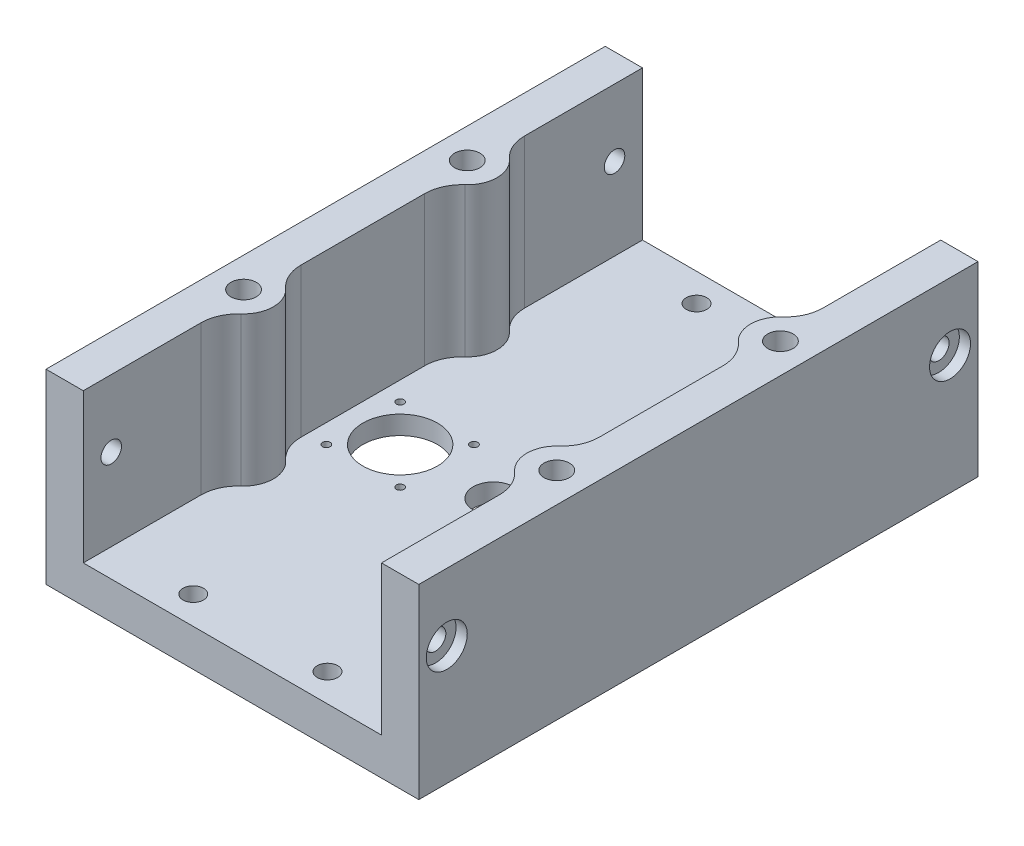
SolidWorks part; units mm, degrees
material "ERTALON 6SA"
ref_plane "Front Plane" through (0, 0, 0) normal (0, 0, 1) x (1, 0, 0)
ref_plane "Top Plane" through (0, 0, 0) normal (0, 1, 0) x (1, 0, 0)
ref_plane "Right Plane" through (0, 0, 0) normal (1, 0, 0) x (0, 0, -1)
sketch "Sketch1" plane through (0, 0, 0) normal (0, 1, 0) x (1, 0, 0)
  line L1 (-50, 0) -> (50, 0)
  line L2 (-50, 0) -> (-50, 150)
  line L3 (-50, 150) -> (50, 150)
  line L4 (50, 0) -> (50, 150)
  dimension "D1" = 100
  dimension "D2" = 50
  dimension "D3" = 150
extrude "Extrude1" add sketch "Sketch1" against normal blind 10
sketch "Sketch2" plane through (0, 0, 0) normal (0, 1, 0) x (1, 0, 0)
  line L0 (50, 150) -> (-50, 150) construction
  line L1 (-50, 150) -> (-40, 150)
  line L2 (-50, 150) -> (-50, 0)
  line L3 (-50, 0) -> (-40, 0)
  line L4 (-40, 150) -> (-40, 0)
  line L5 (-50, 0) -> (50, 0) construction
  line L6 (-50, 150) -> (-50, 0) construction
  line L7 (50, 0) -> (50, 150) construction
  line L8 (40, 150) -> (50, 150)
  line L9 (40, 150) -> (40, 0)
  line L10 (40, 0) -> (50, 0)
  line L11 (50, 150) -> (50, 0)
  dimension "D1" = 10
  dimension "D2" = 10
extrude "Extrude2" add sketch "Sketch2" along normal blind 40
sketch "Sketch6" plane through (0, 40, 0) normal (0, 1, 0) x (1, 0, 0)
  line L0 (50, 0) -> (50, 150) construction
  line L1 (42, 53) -> (50, 53)
  line L2 (50, 53) -> (50, 37)
  line L3 (50, 37) -> (42, 37)
  line L4 (50, 150) -> (40, 150) construction
  line L5 (42, 113) -> (50, 113)
  line L6 (50, 113) -> (50, 97)
  line L7 (50, 97) -> (42, 97)
  line L8 (40, 0) -> (50, 0) construction
  arc A0 (42, 53) -> (42, 37) centre (42, 45) ccw
  arc A1 (42, 113) -> (42, 97) centre (42, 105) ccw
  point P9 (45, 150)
  dimension "D1" = 8
  dimension "D2" = 45
  dimension "D3" = 45
extrude "Extrude5" add sketch "Sketch6" against normal up to next (50 mm away)
mirror "Mirror2" about plane through (0, 0, 0) normal (1, 0, 0) of "Extrude5"
fillet "Fillet1" radius 10 8 edges at (40, 20, -112.746) (40, 20, -97.254) (40, 20, -52.746) (40, 20, -37.254) (-40, 20, -97.254) (-40, 20, -112.746) (-40, 20, -37.254) (-40, 20, -52.746)
hole_wizard "M8 Tapped Hole1" positions "Sketch13" profile "Sketch12" tap size "M8" standard "ISO"
sketch "Sketch13" plane through (0, 40, 0) normal (0, 1, 0) x (-1, 0, 0)
  arc A0 (-36.6667, -50.9628) -> (-36.6667, -39.0372) centre (-42, -45) ccw construction
  point P0 (-42, -45)
sketch "Sketch12" plane through (42, 40, -45) normal (1, 0, 0) x (0, 0, 1)
  line L0 (0, 0) -> (0, 24.0429)
  line L1 (0, 24.0429) -> (3.4, 22)
  line L2 (3.4, 22) -> (3.4, 0)
  line L5 (3.4, 0) -> (0, 0)
  line L10 (0, 24.0429) -> (-3.4, 22) construction
  line L11 (0, -6.35) -> (0, 107.95) construction
  dimension "Tap Drill Dia." = 6.8
  dimension "Tap Drill Depth" = 22
  dimension "Drill Angle" = 118
cosmetic thread "Hole Thread2" parameters "D1"=16, "D2"=8
pattern_linear "LPattern1" count 2 spacing 60 along (0, 0, -1) count 2 spacing 84 along (-1, 0, 0) of "M8 Tapped Hole1"
ref_plane "Plane2" through (0, 0, -75) normal (0, 0, 1) x (1, 0, 0)
sketch "Sketch16" plane through (0, -10, 0) normal (0, -1, 0) x (1, 0, 0)
  line L1 (-40, -15) -> (40, -15)
  line L2 (-40, -15) -> (-40, -90)
  line L3 (-40, -90) -> (40, -90)
  line L4 (40, -15) -> (40, -90)
  line L6 (-50, 0) -> (50, 0) construction
  point P4 (0, -15)
  dimension "D1" = 75
  dimension "D2" = 80
  dimension "D3" = 15
extrude "Extrude8" cut sketch "Sketch16" against normal blind 5
fillet "Fillet2" radius 6 4 edges at (-40, -7.5, -15) (40, -7.5, -15) (-40, -7.5, -90) (40, -7.5, -90)
sketch "Sketch14" plane through (0, -10, 0) normal (0, -1, 0) x (1, 0, 0)
  circle A0 centre (-25, -70) radius 10
  dimension "D1" = 20
  dimension "D2" = 25
  dimension "D3" = 70
hole_wizard "M2.5 Tapped Hole1" positions "3DSketch1" profile "Sketch15" tap size "M2.5" standard "ISO" end condition up to next
sketch3d "3DSketch1"
  line L0 (-25, -10, -70) -> (-25, -10, -3.749) construction
  line L2 (-25, -10, -70) -> (-2.028, -10, -70) construction
  point P0 (-34.9, -10, -60.1)
  dimension "D1" = 9.9
  dimension "D2" = 9.9
cosmetic thread "Hole Thread1" parameters "D2"=2.5
sketch "Sketch15" plane through (-34.9, -10, -60.1) normal (1, 0, 0) x (0, 0, -1)
  line L0 (0, 0) -> (0, 10.0011)
  line L1 (0, 10.0011) -> (1.025, 10.0011)
  line L2 (1.025, 10.0011) -> (1.025, 0)
  line L5 (1.025, 0) -> (0, 0)
  line L11 (0, -6.35) -> (0, 107.95) construction
  dimension "Thru Tap Drill Dia." = 2.05
  dimension "Thru Tap Drill Depth" = 10.0011
extrude "Extrude7" cut sketch "Sketch14" against normal up to next
pattern_linear "LPattern2" count 2 spacing 19.8 along (1, 0, 0) count 2 spacing 19.8 along (0, 0, -1) of "M2.5 Tapped Hole1"
mirror "Mirror4" about plane through (0, 0, 0) normal (1, 0, 0) of "LPattern2", "Extrude7", "M2.5 Tapped Hole1"
hole_wizard "Ø10.8 (10.8) Diameter Hole1" positions "Sketch18" profile "Sketch17" hole size "Ø10.8" standard "ISO" end condition up to next
sketch "Sketch18" plane through (0, -5, 0) normal (0, -1, 0) x (1, 0, 0)
  circle A8 centre (25, -70) radius 10 construction
  point P0 (0, -70)
  dimension "D1" = 0
sketch "Sketch17" plane through (0, -5, -70) normal (1, 0, 0) x (0, 0, -1)
  line L0 (0, 0) -> (0, 5)
  line L1 (0, 5) -> (5.4, 5)
  line L2 (5.4, 5) -> (5.4, 0)
  line L5 (5.4, 0) -> (0, 0)
  line L11 (0, -6.35) -> (0, 107.95) construction
  dimension "Thru Hole Dia." = 10.8
  dimension "Thru Hole Depth" = 5
hole_wizard "CBORE for M5 Hex Socket Head Cap Screw1" positions "Sketch23" profile "Sketch22" counterbore size "M5" standard "ISO" end condition up to next
sketch "Sketch23" plane through (-50, 0, 0) normal (-1, 0, 0) x (0, 0, 1)
  line L0 (-150, -10) -> (0, -10) construction
  line L2 (0, -10) -> (0, 40) construction
  point P0 (-7.5, 22)
  dimension "D1" = 32
  dimension "D2" = 7.5
sketch "Sketch22" plane through (-50, 22, -7.5) normal (0, 1, 0) x (0, 0, 1)
  line L0 (0, 0) -> (0, 10.001)
  line L1 (0, 10.001) -> (2.75, 10.001)
  line L3 (2.75, 10.001) -> (2.75, 3)
  line L4 (2.75, 3) -> (5.5, 3)
  line L5 (5.5, 3) -> (5.5, 0)
  line L7 (5.5, 0) -> (0, 0)
  line L11 (0, -6.35) -> (0, 107.95) construction
  dimension "Thru Hole Dia." = 5.5
  dimension "Thru Hole Depth" = 10.001
  dimension "C'Bore Dia." = 11
  dimension "C'Bore Depth" = 3
mirror "Mirror5" about plane through (0, 0, 0) normal (1, 0, 0) of "CBORE for M5 Hex Socket Head Cap Screw1"
hole_wizard "CBORE for M5 Hex Socket Head Cap Screw2" positions "Sketch25" profile "Sketch24" counterbore size "M5" standard "ISO" end condition up to next
sketch "Sketch25" plane through (0, -10, 0) normal (0, -1, 0) x (1, 0, 0)
  line L0 (-40, 0) -> (-40, -31.5836) construction
  line L1 (40, -31.5836) -> (40, 0) construction
  line L2 (-40, 0) -> (40, 0) construction
  point P0 (-18, -7.5)
  point P1 (18, -7.5)
  dimension "D1" = 22
  dimension "D2" = 22
  dimension "D3" = 7.5
sketch "Sketch24" plane through (-18, -10, -7.5) normal (1, 0, 0) x (0, 0, -1)
  line L0 (0, 0) -> (0, 10.0011)
  line L1 (0, 10.0011) -> (2.75, 10.0011)
  line L3 (2.75, 10.0011) -> (2.75, 5)
  line L4 (2.75, 5) -> (5, 5)
  line L5 (5, 5) -> (5, 0)
  line L7 (5, 0) -> (0, 0)
  line L11 (0, -6.35) -> (0, 107.95) construction
  dimension "Thru Hole Dia." = 5.5
  dimension "Thru Hole Depth" = 10.0011
  dimension "C'Bore Dia." = 10
  dimension "C'Bore Depth" = 5
mirror "Mirror6" about plane through (0, 0, -75) normal (0, 0, 1) of "CBORE for M5 Hex Socket Head Cap Screw2", "Mirror5", "CBORE for M5 Hex Socket Head Cap Screw1"
